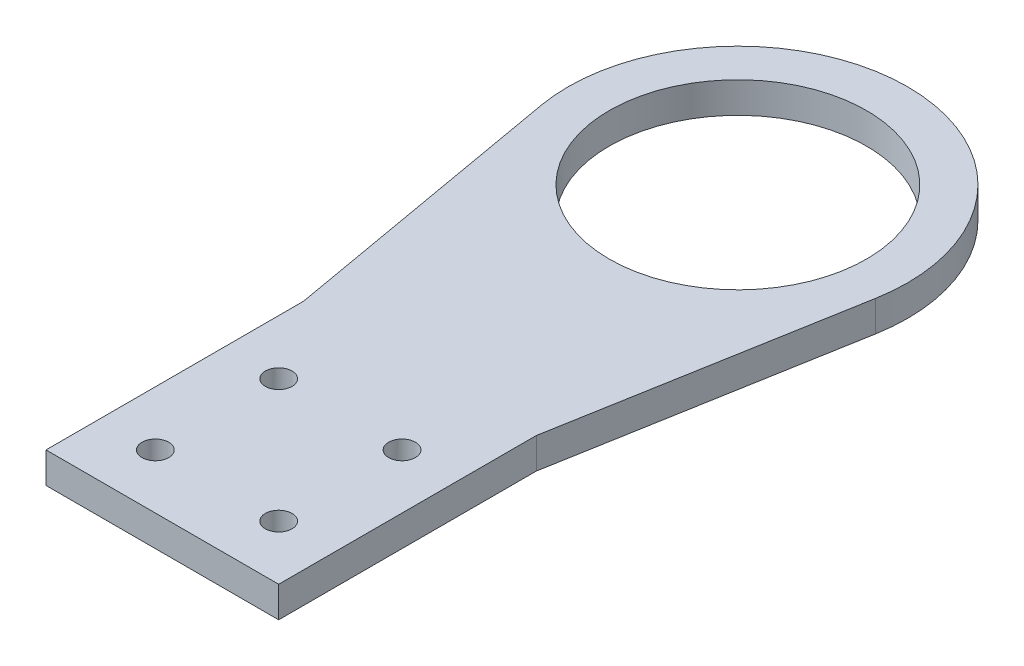
SolidWorks part; units mm, degrees
ref_plane "Front Plane" through (0, 0, 0) normal (0, 0, 1) x (1, 0, 0)
ref_plane "Top Plane" through (0, 0, 0) normal (0, 1, 0) x (1, 0, 0)
ref_plane "Right Plane" through (0, 0, 0) normal (1, 0, 0) x (0, 0, -1)
sketch "Sketch1" plane through (0, 0, 0) normal (0, 1, 0) x (1, 0, 0)
  line L0 (-35.941, 0) -> (35.941, 0)
  line L1 (-19.05, 16.891) -> (19.05, 16.891) construction
  line L2 (-19.05, 16.891) -> (-19.05, 54.991) construction
  line L3 (-19.05, 54.991) -> (19.05, 54.991) construction
  line L4 (19.05, 16.891) -> (19.05, 54.991) construction
  line L5 (35.941, 0) -> (35.941, 79.5783)
  line L6 (35.941, 79.5783) -> (51.6542, 168.692)
  line L7 (-35.941, 0) -> (-35.941, 79.5783)
  line L8 (-35.941, 79.5783) -> (-51.6542, 168.692)
  line L9 (-19.05, 16.891) -> (-35.941, 16.891) construction
  line L10 (-19.05, 16.891) -> (-19.05, 0) construction
  arc A0 (51.6542, 168.692) -> (-51.6542, 168.692) centre (0, 177.8) ccw
  circle A1 centre (0, 177.8) radius 39.751
  circle A2 centre (-19.05, 54.991) radius 4.1275
  circle A3 centre (19.05, 54.991) radius 4.1275
  circle A4 centre (19.05, 16.891) radius 4.1275
  circle A5 centre (-19.05, 16.891) radius 4.1275
  point P13 (0, 0)
  point P15 (0, 16.891)
  dimension "D3" = 79.502
  dimension "D4" = 12.7
  dimension "D7" = 8.255
  dimension "D1" = 38.1
  dimension "D2" = 71.882
  dimension "D5" = 177.8
  dimension "D6" = 20
  dimension "D8" = 2
  dimension "D9" = 2
extrude "Boss-Extrude1" add sketch "Sketch1" along normal blind 9.525
